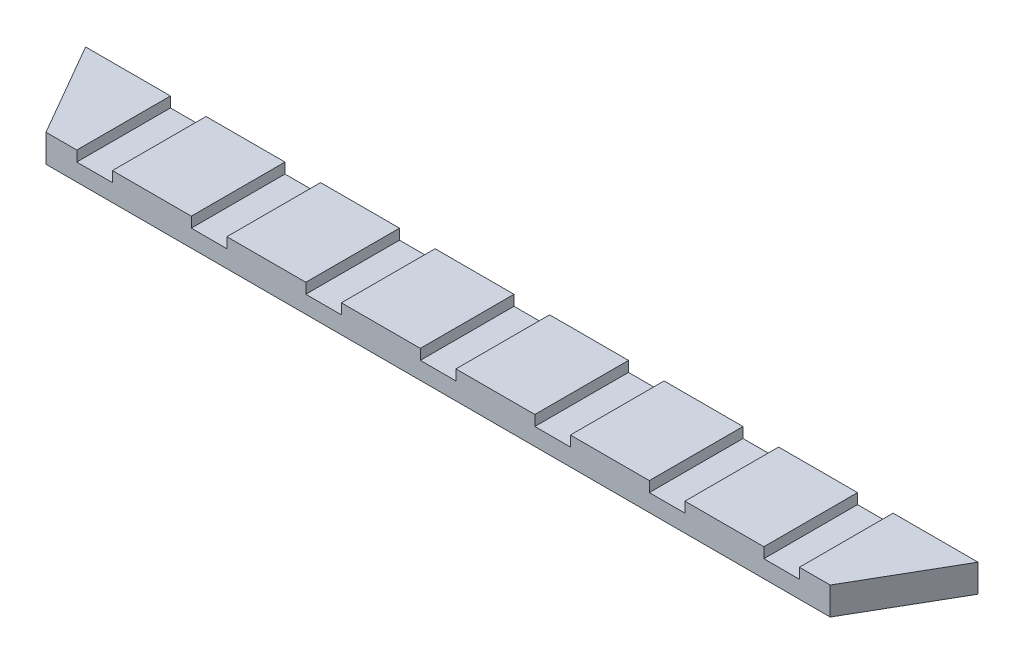
SolidWorks part; units mm, degrees
ref_plane "Front Plane" through (0, 0, 0) normal (0, 0, 1) x (1, 0, 0)
ref_plane "Top Plane" through (0, 0, 0) normal (0, 1, 0) x (1, 0, 0)
ref_plane "Right Plane" through (0, 0, 0) normal (1, 0, 0) x (0, 0, -1)
sketch "Sketch1" plane through (0, 0, 0) normal (0, 1, 0) x (1, 0, 0)
  line L1 (-113, -12.6289) -> (113, -12.6289)
  line L2 (-113, -12.6289) -> (-128.5885, 14.3711)
  line L3 (-128.5885, 14.3711) -> (128.5885, 14.3711)
  line L4 (113, -12.6289) -> (128.5885, 14.3711)
  line L5 (-113, -12.6289) -> (128.5885, 14.3711) construction
  line L6 (-128.5885, 14.3711) -> (113, -12.6289) construction
  point P0 (0, 0)
  dimension "D1" = 226
  dimension "D2" = 27
  dimension "D3" = 120
extrude "Boss-Extrude1" add sketch "Sketch1" along normal blind 8
sketch "Sketch4" plane through (0, 8, 0) normal (0, 1, 0) x (1, 0, 0)
  line L0 (-120.7942, 0.8711) -> (120.7942, 0.8711) construction
  line L1 (-71.1291, 14.3711) -> (-71.1291, -12.6289)
  line L2 (-71.1291, -12.6289) -> (-60.8709, -12.6289)
  line L3 (-60.8709, 14.3711) -> (-60.8709, -12.6289)
  line L4 (-71.1291, 14.3711) -> (-60.8709, -12.6289) construction
  line L9 (-128.5885, 14.3711) -> (-113, -12.6289) construction
  line L10 (113, -12.6289) -> (128.5885, 14.3711) construction
  line L11 (-113, -12.6289) -> (113, -12.6289) construction
  line L16 (-104.1291, 14.3711) -> (-93.8709, 14.3711)
  line L17 (-104.1291, 14.3711) -> (-104.1291, -12.6289)
  line L22 (-104.1291, -12.6289) -> (-93.8709, -12.6289)
  line L23 (-93.8709, 14.3711) -> (-93.8709, -12.6289)
  line L28 (-104.1291, 14.3711) -> (-93.8709, -12.6289) construction
  line L29 (-104.1291, -12.6289) -> (-93.8709, 14.3711) construction
  line L30 (-71.1291, -12.6289) -> (-60.8709, 14.3711) construction
  line L31 (-71.1291, 14.3711) -> (-60.8709, 14.3711)
  line L32 (-38.1291, 14.3711) -> (-38.1291, -12.6289)
  line L33 (-38.1291, -12.6289) -> (-27.8709, -12.6289)
  line L34 (-27.8709, 14.3711) -> (-27.8709, -12.6289)
  line L35 (-38.1291, 14.3711) -> (-27.8709, -12.6289) construction
  line L36 (-38.1291, -12.6289) -> (-27.8709, 14.3711) construction
  line L37 (-38.1291, 14.3711) -> (-27.8709, 14.3711)
  line L38 (-5.1291, 14.3711) -> (-5.1291, -12.6289)
  line L39 (-5.1291, -12.6289) -> (5.1291, -12.6289)
  line L40 (5.1291, 14.3711) -> (5.1291, -12.6289)
  line L41 (-5.1291, 14.3711) -> (5.1291, -12.6289) construction
  line L42 (-5.1291, -12.6289) -> (5.1291, 14.3711) construction
  line L43 (-5.1291, 14.3711) -> (5.1291, 14.3711)
  line L44 (27.8709, 14.3711) -> (27.8709, -12.6289)
  line L45 (27.8709, -12.6289) -> (38.1291, -12.6289)
  line L46 (38.1291, 14.3711) -> (38.1291, -12.6289)
  line L47 (27.8709, 14.3711) -> (38.1291, -12.6289) construction
  line L48 (27.8709, -12.6289) -> (38.1291, 14.3711) construction
  line L49 (27.8709, 14.3711) -> (38.1291, 14.3711)
  line L50 (60.8709, 14.3711) -> (60.8709, -12.6289)
  line L51 (60.8709, -12.6289) -> (71.1291, -12.6289)
  line L52 (71.1291, 14.3711) -> (71.1291, -12.6289)
  line L53 (60.8709, 14.3711) -> (71.1291, -12.6289) construction
  line L54 (60.8709, -12.6289) -> (71.1291, 14.3711) construction
  line L55 (60.8709, 14.3711) -> (71.1291, 14.3711)
  line L56 (93.8709, 14.3711) -> (93.8709, -12.6289)
  line L57 (93.8709, -12.6289) -> (104.1291, -12.6289)
  line L58 (104.1291, 14.3711) -> (104.1291, -12.6289)
  line L59 (93.8709, 14.3711) -> (104.1291, -12.6289) construction
  line L60 (93.8709, -12.6289) -> (104.1291, 14.3711) construction
  line L61 (93.8709, 14.3711) -> (104.1291, 14.3711)
  point P2 (0, -12.6289)
  point P7 (-99, 0.8711)
  dimension "D1" = 10.2582
  dimension "D2" = 7
extrude "Cut-Extrude1" cut sketch "Sketch4" against normal blind 3
equation "\"FullCut\"= 8"
equation "\"FullSpacing\" = 33"
equation "\"CornersHeight\"= 15"
equation "\"EdgesHeight\"= 16"
equation "\"FullSingle\"= 4"
equation "\"FullSingleSpacing\"= 16.5"
